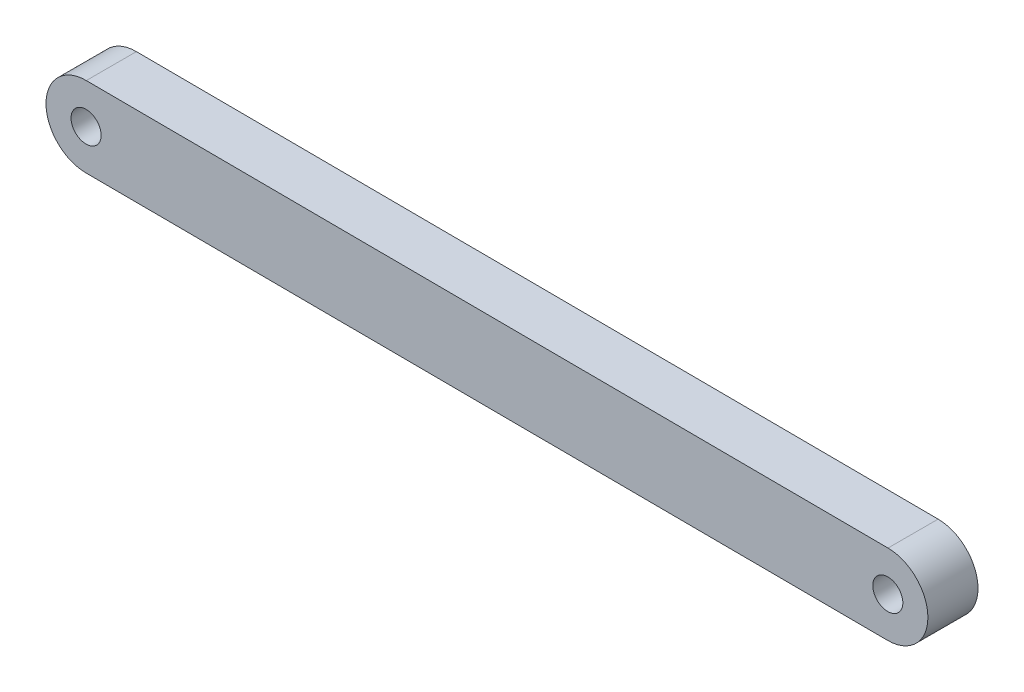
SolidWorks part; units mm, degrees
ref_plane "Front Plane" through (0, 0, 0) normal (0, 0, 1) x (1, 0, 0)
ref_plane "Top Plane" through (0, 0, 0) normal (0, 1, 0) x (1, 0, 0)
ref_plane "Right Plane" through (0, 0, 0) normal (1, 0, 0) x (0, 0, -1)
sketch "Sketch1" plane through (0, 0, 0) normal (0, 0, 1) x (1, 0, 0)
  line L0 (0, 0) -> (80, -0.4001) construction
  line L4 (0.02, 3.9999) -> (80.02, 3.5999)
  line L5 (-0.02, -3.9999) -> (79.98, -4.4)
  arc A4 (0.02, 3.9999) -> (-0.02, -3.9999) centre (0, 0) ccw
  arc A5 (79.98, -4.4) -> (80.02, 3.5999) centre (80, -0.4001) ccw
  circle A6 centre (0, 0) radius 1.5
  circle A7 centre (80, -0.4001) radius 1.5
  point P2 (40, -0.2)
  dimension "D3" = 3
  dimension "D1" = 8
  dimension "D2" = 80
extrude "Boss-Extrude1" add sketch "Sketch1" along normal blind 5
